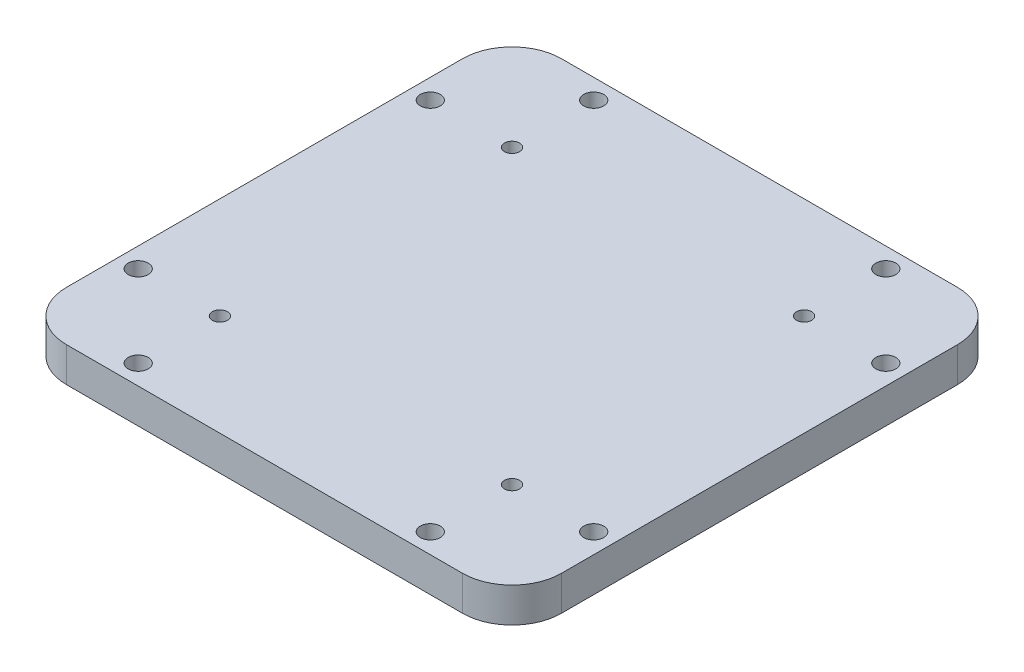
SolidWorks part; units mm, degrees
material "Thornel Mat VMA"
ref_plane "前视基准面" through (0, 0, 0) normal (0, 0, 1) x (1, 0, 0)
ref_plane "上视基准面" through (0, 0, 0) normal (0, 1, 0) x (1, 0, 0)
ref_plane "右视基准面" through (0, 0, 0) normal (1, 0, 0) x (0, 0, -1)
other "Configuration Table"
sketch "草图1" plane through (0, 0, 0) normal (0, 1, 0) x (1, 0, 0)
  line L1 (0, 0) -> (100, 0)
  line L2 (0, 0) -> (0, 100)
  line L3 (0, 100) -> (100, 100)
  line L4 (100, 0) -> (100, 100)
  dimension "D1" = 100
  dimension "D2" = 100
extrude "凸台-拉伸1" add sketch "草图1" along normal blind 7 contours L2 L3 L4 L1
fillet "圆角1" radius 10 4 edges at (0, 3.5, -100) (100, 3.5, -100) (100, 3.5, 0) (0, 3.5, 0)
sketch "草图2" plane through (0, 7, 0) normal (0, 1, 0) x (1, 0, 0)
  line L0 (100, 50) -> (0, 50)
  line L1 (0, 100) -> (20.5, 100)
  line L2 (0, 100) -> (0, 79.5)
  line L3 (0, 79.5) -> (20.5, 79.5)
  line L4 (20.5, 100) -> (20.5, 79.5)
  line L5 (100, 10) -> (100, 90) construction
  line L6 (0, 10) -> (0, 90) construction
  line L7 (50, 0) -> (50, 100)
  line L8 (10, 0) -> (90, 0) construction
  line L9 (10, 100) -> (90, 100) construction
  line L10 (20.5, 100) -> (20.5, 96)
  line L11 (0, 79.5) -> (4, 79.5)
  circle A0 centre (20.5, 79.5) radius 1.52
  circle A1 centre (20.5, 96) radius 2.02
  circle A2 centre (4, 79.5) radius 2.02
  circle A3 centre (20.5, 4) radius 2.02
  circle A4 centre (20.5, 20.5) radius 1.52
  circle A5 centre (4, 20.5) radius 2.02
  circle A6 centre (79.5, 96) radius 2.02
  circle A7 centre (79.5, 4) radius 2.02
  circle A8 centre (79.5, 20.5) radius 1.52
  circle A9 centre (96, 20.5) radius 2.02
  circle A10 centre (96, 79.5) radius 2.02
  circle A11 centre (79.5, 79.5) radius 1.52
  dimension "D3" = 4
  dimension "D4" = 4
  dimension "D1" = 20.5
  dimension "D2" = 20.5
extrude "切除-拉伸2" cut sketch "草图2" against normal blind 13 contours L4 A0 L3 | L11 A2 L3 | L3 A2 L11 | L10 A1 L4 | L4 A1 L10 | L3 A0 L4 | A11 | A6 | A10 | A8 | A9 | A7 | A4 | A5 | A3
